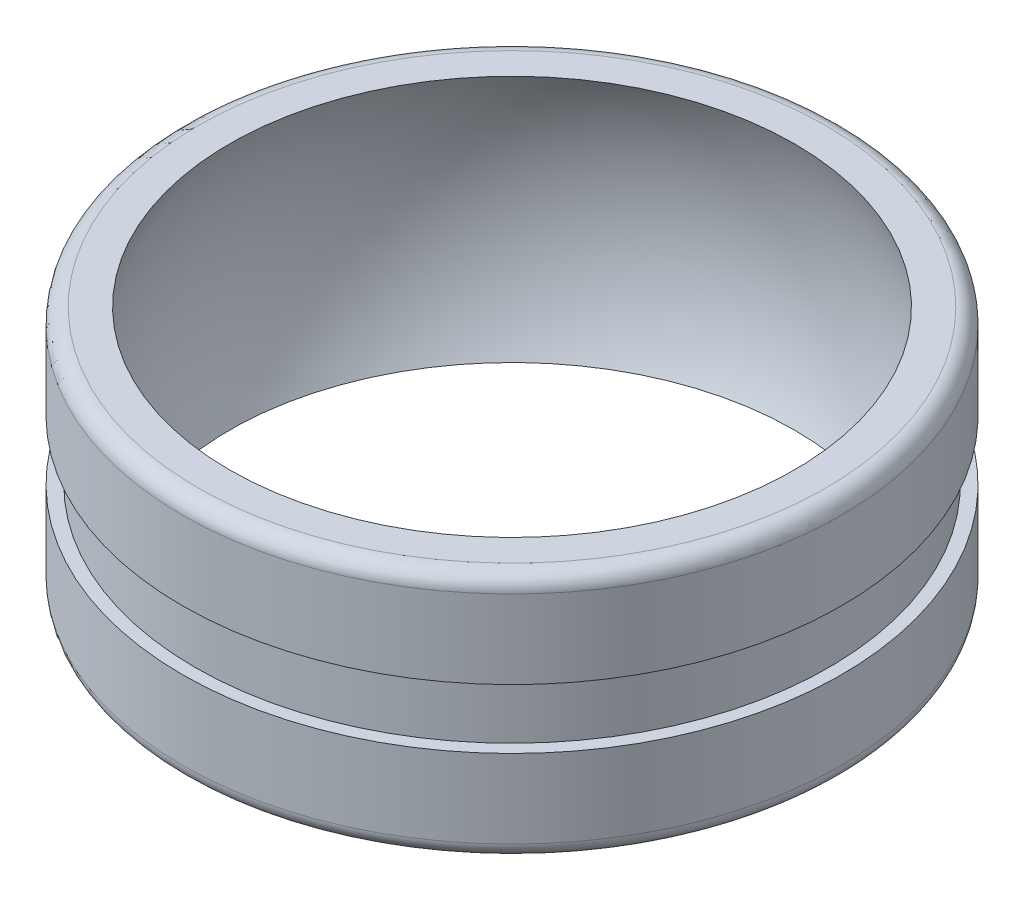
SolidWorks part; units mm, degrees
ref_plane "Спереди" through (0, 0, 0) normal (0, 0, 1) x (1, 0, 0)
ref_plane "Сверху" through (0, 0, 0) normal (0, 1, 0) x (1, 0, 0)
ref_plane "Справа" through (0, 0, 0) normal (1, 0, 0) x (0, 0, -1)
sketch "Sketch1" plane through (0, 0, 0) normal (1, 0, 0) x (0, 0, -1)
  line L0 (0, 7.9) -> (0, -7.9) construction
  line L1 (21, 7.9) -> (21, 1.9)
  line L2 (18, -7.9) -> (21, -7.9)
  line L3 (21, -7.9) -> (21, 7.9) construction
  line L4 (21, 7.9) -> (18, 7.9)
  line L5 (21, 1.9) -> (20.2, 1.9)
  line L6 (20.2, 1.9) -> (20.2, -1.9)
  line L7 (20.2, -1.9) -> (21, -1.9)
  line L8 (21, -1.9) -> (21, -7.9)
  line L9 (19.8263, 0) -> (0, 0) construction
  arc A0 (18, 7.9) -> (18, -7.9) centre (1.8263, 0) cw
  point P14 (0, 0)
  point P16 (0, 0)
  dimension "D1" = 18
  dimension "D2" = 15.8
  dimension "D3" = 3
  dimension "D4" = 21
  dimension "D5" = 6
  dimension "D6" = 0.8
revolve "Revolve1" add sketch "Sketch1" angle 360 about L0
fillet "Fillet1" radius 1 2 edges at (0, -7.9, 21) (0, 7.9, 21)
